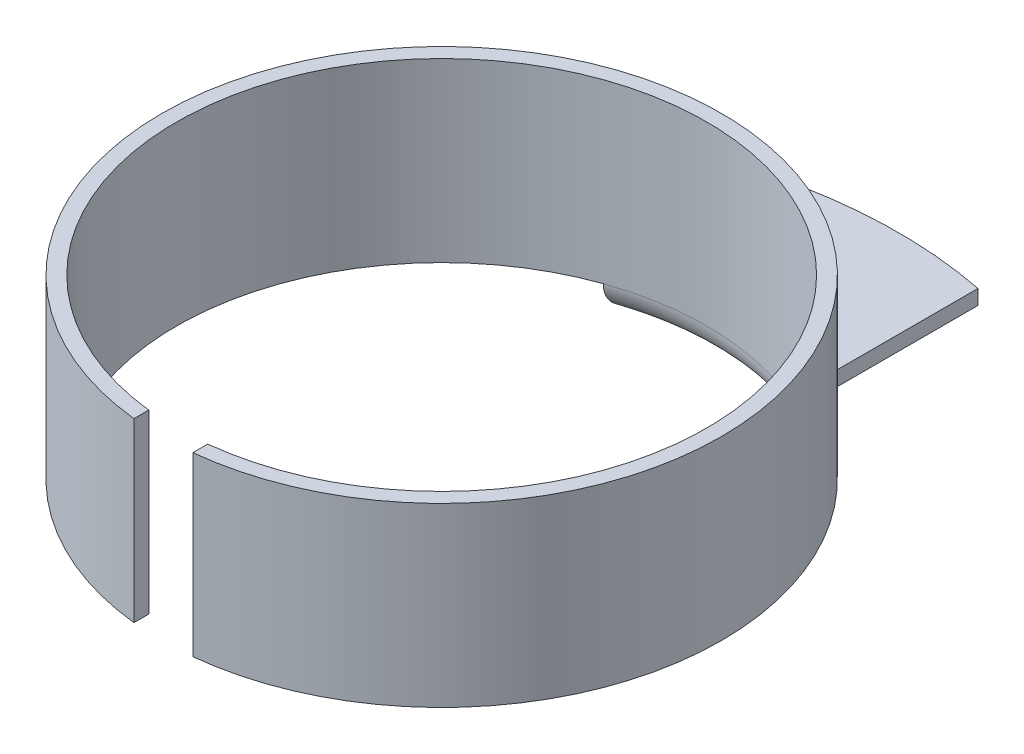
SolidWorks part; units mm, degrees
ref_plane "Спереди" through (0, 0, 0) normal (0, 0, 1) x (1, 0, 0)
ref_plane "Сверху" through (0, 0, 0) normal (0, 1, 0) x (1, 0, 0)
ref_plane "Справа" through (0, 0, 0) normal (1, 0, 0) x (0, 0, -1)
sketch "Эскиз1" plane through (0, 0, 0) normal (0, 0, 1) x (1, 0, 0)
  line L0 (4.5, 0) -> (4.5, 3.5)
  line L2 (4.75, 3.5) -> (4.75, 0.25)
  line L3 (4.75, 0.25) -> (7.75, 0.25)
  line L4 (7.75, 0.25) -> (7.75, 0)
  line L5 (7.75, 0) -> (4.5, 0)
  line L6 (0, 0) -> (0, 7.1363) construction
  line L8 (4.5, 3.5) -> (4.75, 3.5)
  dimension "D1" = 9
  dimension "D2" = 9.5
  dimension "D3" = 15.5
  dimension "D4" = 0.25
  dimension "D5" = 3.5
revolve "Повернуть1" add sketch "Эскиз1" angle 360 about L6
sketch "Эскиз2" plane through (0, 0, 0) normal (0, -1, 0) x (1, 0, 0)
  line L0 (-1.5, -7.6035) -> (-1.5, -2.4)
  line L1 (-1.5, -2.4) -> (1.5, -2.4)
  line L2 (1.5, -2.4) -> (1.5, -7.6035)
  circle A0 centre (0, 0) radius 7.75 construction
  arc A1 (1.5, -7.6035) -> (-1.5, -7.6035) centre (0, 0) ccw
  circle M1 centre (0, 0) radius 7.75
  circle M2 centre (0, 0) radius 4.5
  dimension "D2" = 2.4
  dimension "D1" = 3
extrude "Вырез-Вытянуть1" cut sketch "Эскиз2" against normal blind 0.5 contours L1 L2 L0 M1 M2
sketch "Эскиз3" plane through (0, 3.5, 0) normal (0, 1, 0) x (1, 0, 0)
  line L0 (-0.5, -4.4721) -> (-0.5, -4.7236)
  line L1 (0.5, -4.4721) -> (0.5, -4.7236)
  circle A0 centre (0, 0) radius 4.5 construction
  circle A1 centre (0, 0) radius 4.75 construction
  circle M1 centre (0, 0) radius 4.5
  circle M2 centre (0, 0) radius 4.75
  dimension "D1" = 1
extrude "Вырез-Вытянуть2" cut sketch "Эскиз3" against normal through all contours L1 L0 M1 M2
fillet "Скругление1" radius 0.25 1 edges at (0, 0.25, -4.75)
fillet "Скругление2" radius 0.5 1 edges at (0, 0, -4.5)
